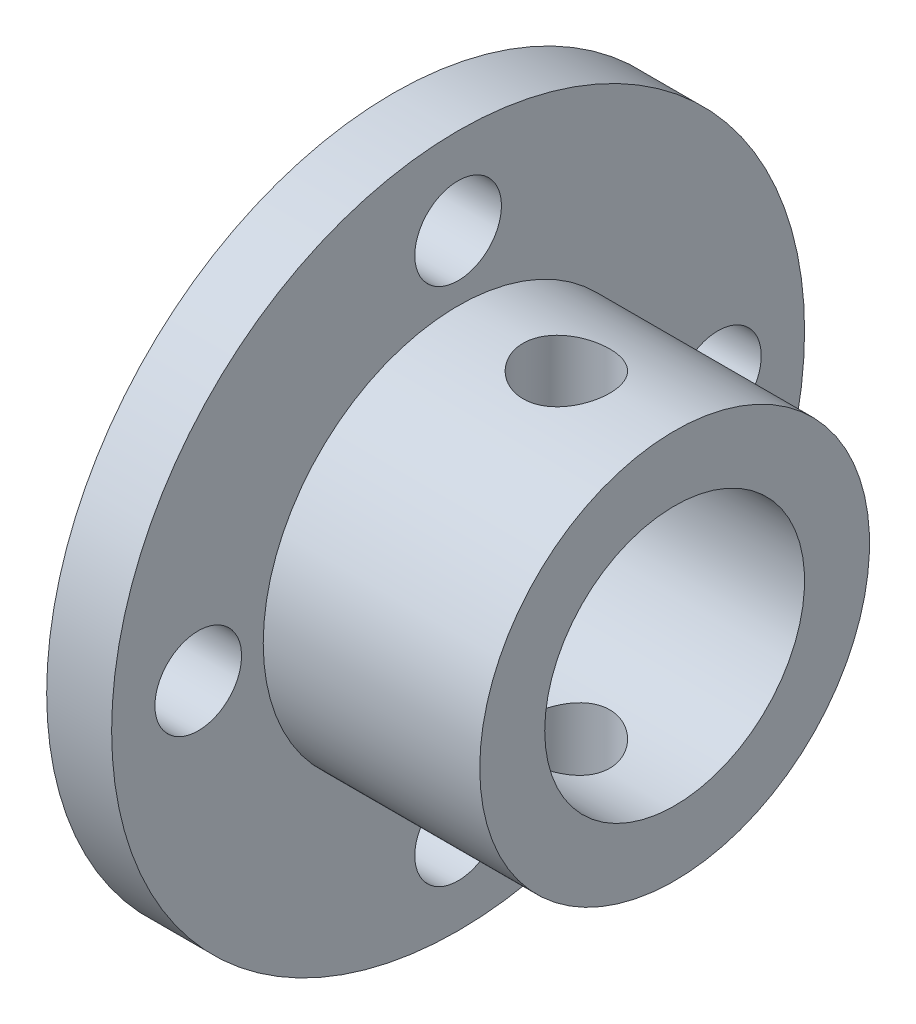
SolidWorks part; units mm, degrees
ref_plane "Front Plane" through (0, 0, 0) normal (0, 0, 1) x (1, 0, 0)
ref_plane "Top Plane" through (0, 0, 0) normal (0, 1, 0) x (1, 0, 0)
ref_plane "Right Plane" through (0, 0, 0) normal (1, 0, 0) x (0, 0, -1)
sketch "Sketch1" plane through (0, 0, 0) normal (0, 0, 1) x (1, 0, 0)
  line L0 (0, 0) -> (0, 6) construction
  line L1 (0, 0) -> (21.7351, 0) construction
  line L2 (0, 6) -> (0, 16)
  line L3 (0, 16) -> (3, 16)
  line L4 (3, 16) -> (3, 9)
  line L5 (3, 9) -> (13, 9)
  line L6 (13, 9) -> (13, 6)
  line L7 (13, 6) -> (0, 6)
  dimension "D1" = 6
  dimension "D2" = 13
  dimension "D3" = 9
  dimension "D4" = 16
  dimension "D5" = 10
revolve "Revolve1" add sketch "Sketch1" angle 360 about L1
sketch "Sketch2" plane through (0, 0, 0) normal (-1, 0, 0) x (0, 0, 1)
  circle A0 centre (0, 0) radius 12
  circle A1 centre (0, 12) radius 2
  circle A2 centre (12, 0) radius 2
  circle A3 centre (0, -12) radius 2
  circle A4 centre (-12, 0) radius 2
  point P14 (0, 0)
  dimension "D1" = 24
  dimension "D2" = 4
  dimension "D3" = 4
extrude "Cut-Extrude1" cut sketch "Sketch2" against normal through all contours A1 | A4 | A3 | A2
sketch "Sketch3" plane through (0, 0, 0) normal (0, 1, 0) x (1, 0, 0)
  line L0 (13, 0) -> (3, 0) construction
  line L1 (13, -9) -> (13, 9) construction
  line L2 (3, -16) -> (3, 16) construction
  circle A0 centre (8, 0) radius 2
  dimension "D1" = 4
extrude "Cut-Extrude2" cut sketch "Sketch3" against normal through all both and the other way through all
